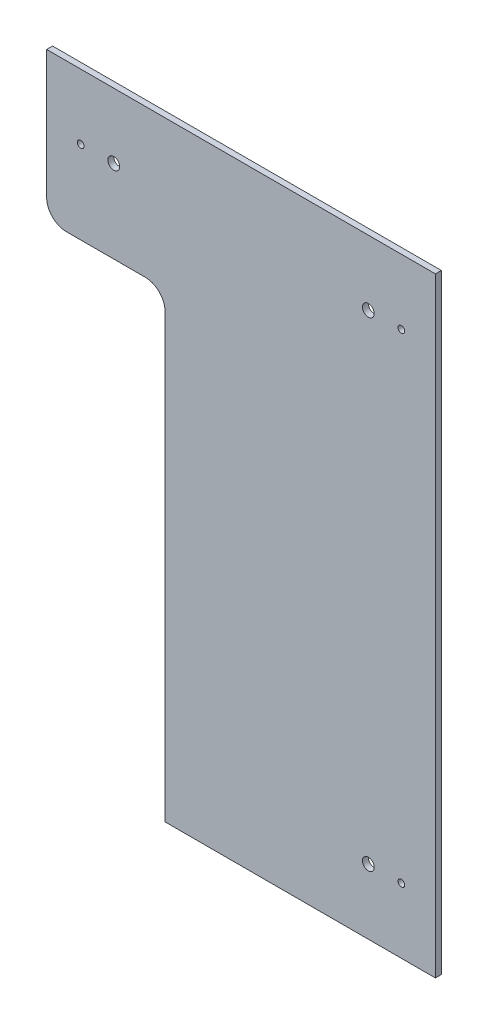
SolidWorks part; units mm, degrees
ref_plane "Plan de face" through (0, 0, 0) normal (0, 0, 1) x (1, 0, 0)
ref_plane "Plan de dessus" through (0, 0, 0) normal (0, 1, 0) x (1, 0, 0)
ref_plane "Plan de droite" through (0, 0, 0) normal (1, 0, 0) x (0, 0, -1)
sketch "Esquisse1" plane through (0, 0, 0) normal (0, 0, 1) x (1, 0, 0)
  line L0 (81.25, 121.5) -> (81.25, 0) construction
  line L1 (-98.5, -154.5) -> (98.5, -154.5)
  line L2 (-98.5, -154.5) -> (-98.5, 154.5)
  line L3 (-98.5, 154.5) -> (98.5, 154.5)
  line L4 (98.5, -154.5) -> (98.5, 154.5)
  line L5 (-98.5, -154.5) -> (98.5, 154.5) construction
  line L6 (-98.5, 154.5) -> (98.5, -154.5) construction
  line L7 (81.25, 0) -> (0, 0) construction
  line L8 (81.25, 121.5) -> (64.5, 121.5) construction
  line L9 (0, 0) -> (0, -154.5) construction
  circle A0 centre (81.25, 121.5) radius 1.7
  circle A2 centre (64.5, 121.5) radius 3
  circle A3 centre (81.25, -121.5) radius 1.7
  circle A4 centre (64.5, -121.5) radius 3
  circle A5 centre (-81.25, -121.5) radius 1.7
  circle A6 centre (-64.5, -121.5) radius 3
  circle A7 centre (-81.25, 121.5) radius 1.7
  circle A8 centre (-64.5, 121.5) radius 3
  point P0 (0, 0)
  dimension "D2" = 3.4
  dimension "D5" = 6
  dimension "D1" = 309
  dimension "D3" = 33
  dimension "D4" = 197
  dimension "D6" = 16.75
  dimension "D7" = 81.25
extrude "Boss.-Extru.1" add sketch "Esquisse1" along normal blind 3
sketch "Esquisse2" plane through (0, 0, 3) normal (0, 0, 1) x (1, 0, 0)
  line L0 (-98.5, 154.5) -> (-98.5, -154.5) construction
  line L1 (-98.5, 79.5) -> (-38.5, 79.5)
  line L2 (-98.5, 79.5) -> (-98.5, -154.5)
  line L3 (-98.5, -154.5) -> (-38.5, -154.5)
  line L4 (-38.5, 79.5) -> (-38.5, -154.5)
  line L5 (-98.5, -154.5) -> (98.5, -154.5) construction
  line L6 (98.5, 154.5) -> (-98.5, 154.5) construction
  dimension "D1" = 75
  dimension "D2" = 60
extrude "Enlèv. mat.-Extru.1" cut sketch "Esquisse2" against normal through all
fillet "Congé1" radius 10 2 edges at (-38.5, 79.5, 1.5) (-98.5, 79.5, 1.5)
